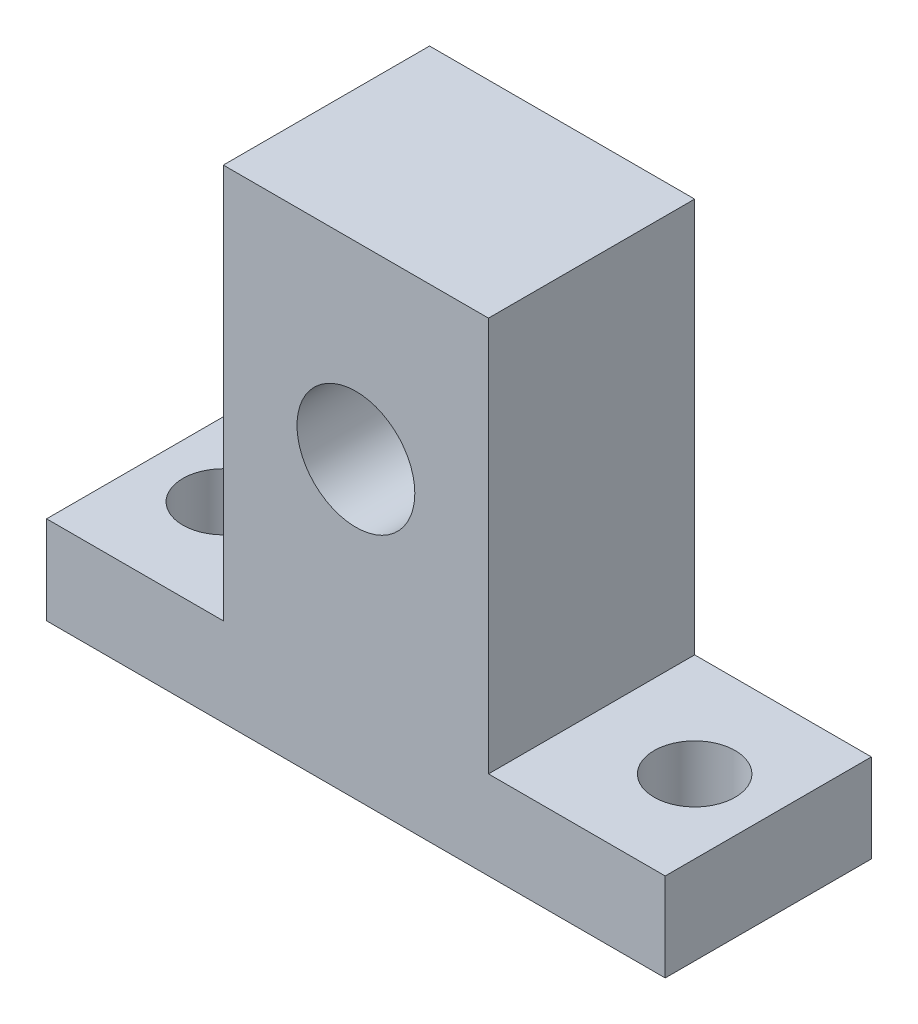
SolidWorks part; units mm, degrees
ref_plane "Front Plane" through (0, 0, 0) normal (0, 0, 1) x (1, 0, 0)
ref_plane "Top Plane" through (0, 0, 0) normal (0, 1, 0) x (1, 0, 0)
ref_plane "Right Plane" through (0, 0, 0) normal (1, 0, 0) x (0, 0, -1)
sketch "Sketch1" plane through (0, 0, 0) normal (0, 0, 1) x (1, 0, 0)
  line L0 (-21, 0) -> (21, 0)
  line L1 (21, 0) -> (21, 6)
  line L2 (21, 6) -> (9, 6)
  line L3 (9, 6) -> (9, 32.8)
  line L4 (9, 32.8) -> (-9, 32.8)
  line L5 (-9, 32.8) -> (-9, 6)
  line L6 (-9, 6) -> (-21, 6)
  line L7 (-21, 6) -> (-21, 0)
  circle A0 centre (0, 20) radius 4
  point P0 (0, 32.8)
  dimension "D5" = 8
  dimension "D1" = 18
  dimension "D2" = 42
  dimension "D3" = 32.8
  dimension "D4" = 6
  dimension "D6" = 20
extrude "Boss-Extrude1" add sketch "Sketch1" along normal blind 14
sketch "Sketch2" plane through (0, 6, 0) normal (0, 1, 0) x (1, 0, 0)
  line L0 (-21, -14) -> (-21, 0) construction
  circle A0 centre (-16, -7) radius 2.75
  circle A1 centre (16, -7) radius 2.75
  point P9 (-21, -7)
  dimension "D3" = 5.5
  dimension "D1" = 16
  dimension "D2" = 32
extrude "Cut-Extrude1" cut sketch "Sketch2" against normal up to surface (6 mm away) up to face at (0, 0, 7)
